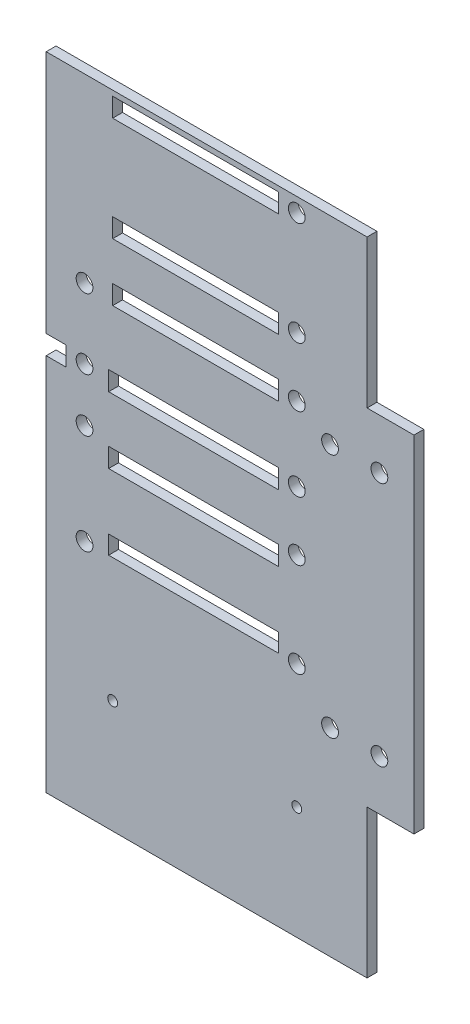
SolidWorks part; units mm, degrees
ref_plane "Plan de face" through (0, 0, 0) normal (0, 0, 1) x (1, 0, 0)
ref_plane "Plan de dessus" through (0, 0, 0) normal (0, 1, 0) x (1, 0, 0)
ref_plane "Plan de droite" through (0, 0, 0) normal (1, 0, 0) x (0, 0, -1)
sketch "Esquisse1" plane through (0, 0, 0) normal (0, 0, 1) x (1, 0, 0)
  line L0 (7, 10.15) -> (7, -59.85)
  line L1 (0, 0) -> (0, -49.7) construction
  line L2 (7, -24.85) -> (-3.4703, -24.85) construction
  line L3 (0, -24.85) -> (-8.0205, -24.85) construction
  line L4 (-12, 10.15) -> (-12, -59.85) construction
  line L5 (7, 10.15) -> (-12, 10.15)
  line L6 (-12, 10.15) -> (-12, -59.85)
  line L7 (-12, -59.85) -> (7, -59.85)
  circle A0 centre (0, 0) radius 1.7
  circle A1 centre (0, -49.7) radius 1.7
  dimension "D1" = 49.7
  dimension "D2" = 7
  dimension "D3" = 70
  dimension "D4" = 0
  dimension "D5" = 12
extrude "Boss.-Extru.1" add sketch "Esquisse1" along normal blind 2
sketch "Esquisse2" plane through (0, 0, 0) normal (0, 0, -1) x (-1, 0, 0)
  line L0 (12, -24.85) -> (-7, -24.85) construction
  line L1 (12, 10.15) -> (12, -59.85) construction
  line L2 (-7, -59.85) -> (-7, 10.15) construction
  line L3 (2.5, -59.85) -> (2.5, 10.15) construction
  line L4 (12, -59.85) -> (-7, -59.85) construction
  line L5 (-7, 10.15) -> (12, 10.15) construction
  line L6 (67.5, -22.7176) -> (67.5, 40.15)
  line L7 (2.5, 40.15) -> (67.5, 40.15)
  line L8 (2.5, 40.15) -> (2.5, -89.85)
  line L9 (2.5, -89.85) -> (67.5, -89.85)
  line L10 (67.5, -26.9824) -> (67.5, -89.85)
  line L11 (67.5, -26.9824) -> (67.5, -22.7176)
  point P19 (2.5, -24.85)
  dimension "D1" = 65
  dimension "D2" = 65
extrude "Boss.-Extru.2" add sketch "Esquisse2" against normal blind 2
sketch "Esquisse3" plane through (0, 0, 0) normal (0, 0, -1) x (-1, 0, 0)
  line L0 (16.7293, -89.85) -> (16.7293, 40.15) construction
  line L1 (2.5, -89.85) -> (67.5, -89.85) construction
  line L2 (2.5, 40.15) -> (67.5, 40.15) construction
  line L3 (8.8257, -66.9686) -> (55.8257, -66.9686) construction
  line L4 (8.8257, -84.4686) -> (55.8257, -84.4686) construction
  line L5 (8.8257, -84.4686) -> (8.8257, -49.4686) construction
  line L6 (8.8257, -49.4686) -> (55.8257, -49.4686) construction
  line L7 (55.8257, -84.4686) -> (55.8257, -49.4686) construction
  line L8 (59.7293, -89.85) -> (59.7293, 40.15) construction
  line L9 (16.7293, -41.85) -> (59.7293, -41.85) construction
  line L10 (16.7293, -10.75) -> (59.7293, -10.75) construction
  line L11 (16.7293, -22.75) -> (54.8452, -22.75) construction
  line L12 (20.4286, -41.85) -> (54.8452, -41.85)
  line L13 (20.4286, -41.85) -> (20.4286, -38.1283)
  line L14 (20.4286, -38.1283) -> (54.8452, -38.1283)
  line L15 (54.8452, -41.85) -> (54.8452, -38.1283)
  line L16 (16.7293, 4.25) -> (54.0293, 4.25) construction
  line L17 (16.7293, 16.25) -> (54.0293, 16.25) construction
  line L18 (16.7293, 37.25) -> (54.0293, 37.25) construction
  line L19 (67.5, -22.7176) -> (67.5, 40.15) construction
  line L20 (20.4286, -22.75) -> (54.8452, -22.75)
  line L21 (20.4286, -22.75) -> (20.4286, -26.644)
  line L22 (20.4286, -26.644) -> (54.8452, -26.644)
  line L23 (54.8452, -22.75) -> (54.8452, -26.644)
  line L24 (20.4286, -13.1753) -> (54.8452, -13.1753)
  line L25 (20.4286, -13.1753) -> (20.4286, -9.2827)
  line L26 (20.4286, -9.2827) -> (54.8452, -9.2827)
  line L27 (54.8452, -13.1753) -> (54.8452, -9.2827)
  line L28 (20.4286, 2.3421) -> (54.0293, 2.3421)
  line L29 (20.4286, 2.3421) -> (20.4286, 6.221)
  line L30 (20.4286, 6.221) -> (54.0293, 6.221)
  line L31 (54.0293, 2.3421) -> (54.0293, 6.221)
  line L32 (20.4286, 14.0826) -> (54.0293, 14.0826)
  line L33 (20.4286, 14.0826) -> (20.4286, 17.9431)
  line L34 (20.4286, 17.9431) -> (54.0293, 17.9431)
  line L35 (54.0293, 14.0826) -> (54.0293, 17.9431)
  line L36 (20.4286, 35.2232) -> (54.0293, 35.2232)
  line L37 (20.4286, 35.2232) -> (20.4286, 39.0838)
  line L38 (20.4286, 39.0838) -> (54.0293, 39.0838)
  line L39 (54.0293, 35.2232) -> (54.0293, 39.0838)
  line L40 (63.4718, -13.1753) -> (67.5, -13.1753)
  line L41 (63.4718, -13.1753) -> (63.4718, -9.2827)
  line L42 (63.4718, -9.2827) -> (67.5, -9.2827)
  line L43 (67.5, -13.1753) -> (67.5, -9.2827)
  circle A0 centre (16.7293, -41.85) radius 1.7
  circle A1 centre (16.7293, -66.9686) radius 1
  circle A2 centre (54.0293, -66.9686) radius 1
  circle A3 centre (16.7293, -22.75) radius 1.7
  circle A4 centre (16.7293, -10.75) radius 1.7
  circle A5 centre (16.7293, 4.25) radius 1.7
  circle A6 centre (16.7293, 16.25) radius 1.7
  circle A7 centre (16.7293, 37.25) radius 1.7
  circle A8 centre (59.7293, -41.85) radius 1.7
  circle A9 centre (59.7293, -21.55) radius 1.7
  circle A10 centre (59.7293, -10.75) radius 1.7
  circle A11 centre (59.7293, 3.45) radius 1.7
  dimension "D1" = 48
  dimension "D4" = 37.3
  dimension "D5" = 19.1
  dimension "D6" = 12
  dimension "D7" = 15
  dimension "D8" = 12
  dimension "D10" = 21
  dimension "D11" = 20.3
  dimension "D12" = 14.2
  dimension "D2" = 35
  dimension "D3" = 47
  dimension "D9" = 43
extrude "Enlèv. mat.-Extru.1" cut sketch "Esquisse3" against normal blind 2
sketch "Esquisse4" plane through (0, 0, 0) normal (0, 0, -1) x (-1, 0, 0)
  line L0 (0, -49.7) -> (10, -49.7) construction
  line L1 (0, 0) -> (10, 0) construction
  circle A0 centre (10, -49.7) radius 1.7
  circle A1 centre (10, 0) radius 1.7
extrude "Enlèv. mat.-Extru.2" cut sketch "Esquisse4" against normal blind 2
